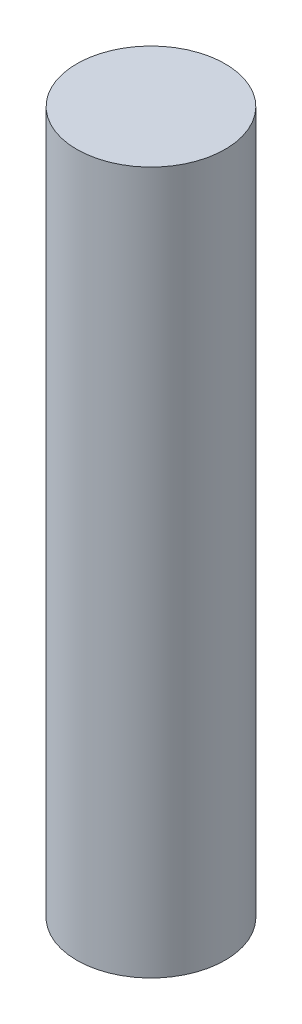
SolidWorks part; units mm, degrees
ref_plane "Front" through (0, 0, 0) normal (0, 0, 1) x (1, 0, 0)
ref_plane "Top" through (0, 0, 0) normal (0, 1, 0) x (1, 0, 0)
ref_plane "Right" through (0, 0, 0) normal (1, 0, 0) x (0, 0, -1)
sketch "Sketch1" plane through (0, 0, 0) normal (0, 1, 0) x (1, 0, 0)
  circle A0 centre (0, 0) radius 32.1945
  dimension "D1" = 64.389
extrude "Boss-Extrude1" add sketch "Sketch1" along normal blind 304.8
